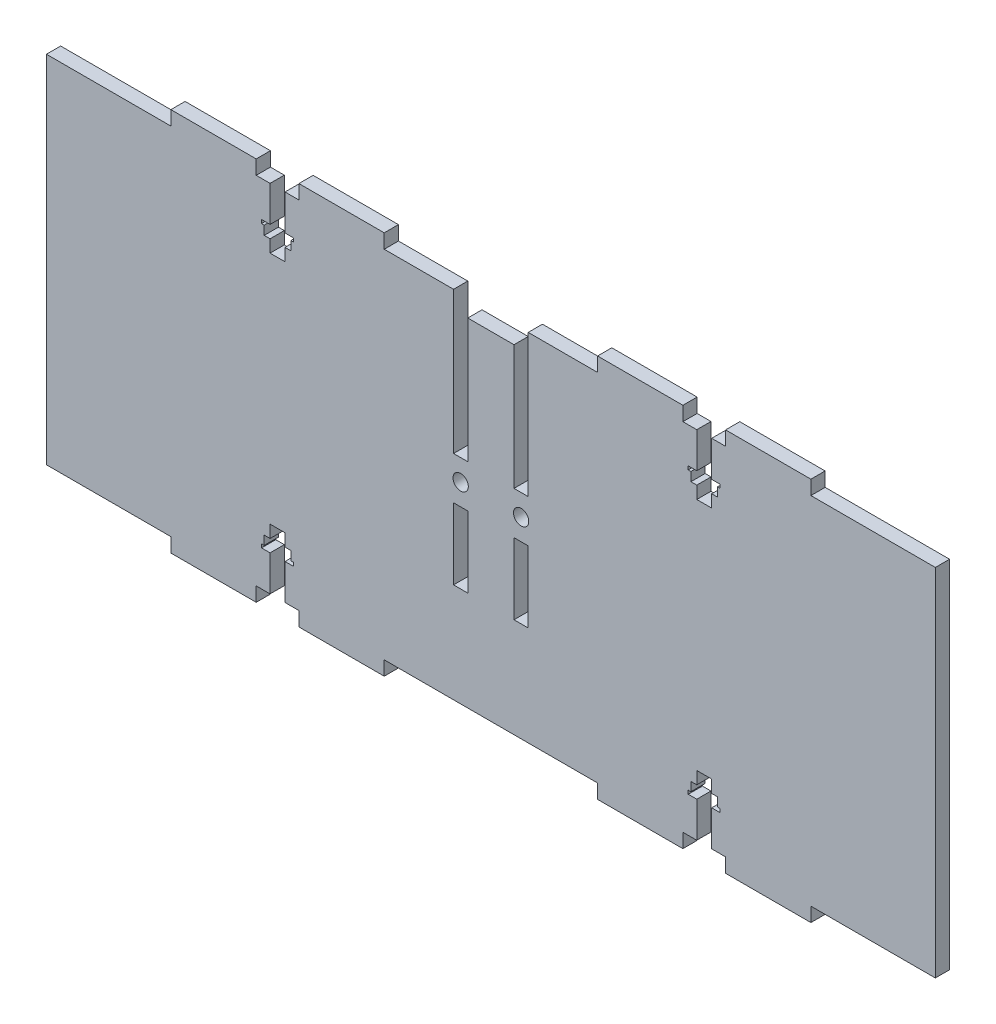
SolidWorks part; units mm, degrees
ref_plane "Front Plane" through (0, 0, 0) normal (0, 0, 1) x (1, 0, 0)
ref_plane "Top Plane" through (0, 0, 0) normal (0, 1, 0) x (1, 0, 0)
ref_plane "Right Plane" through (0, 0, 0) normal (1, 0, 0) x (0, 0, -1)
sketch "Sketch1" plane through (0, 0, 0) normal (0, 0, 1) x (1, 0, 0)
  line L1 (-125, 50) -> (125, 50)
  line L2 (-125, 50) -> (-125, -50)
  line L3 (-125, -50) -> (125, -50)
  line L4 (125, 50) -> (125, -50)
  line L5 (-125, 50) -> (125, -50) construction
  line L6 (-125, -50) -> (125, 50) construction
  point P0 (0, 0)
  dimension "D1" = 250
  dimension "D2" = 100
extrude "Boss-Extrude1" add sketch "Sketch1" along normal blind 4
sketch "Sketch2" plane through (0, -50, 0) normal (0, -1, 0) x (1, 0, 0)
  line L0 (-125, 4) -> (125, 4) construction
  line L1 (-66, 4) -> (-90, 4)
  line L2 (-66, 4) -> (-66, 0)
  line L3 (-66, 0) -> (-90, 0)
  line L4 (-90, 4) -> (-90, 0)
  line L5 (-125, 0) -> (125, 0) construction
  line L7 (-54, 4) -> (-30, 4)
  line L8 (-54, 4) -> (-54, 0)
  line L9 (-54, 0) -> (-30, 0)
  line L10 (-30, 4) -> (-30, 0)
  line L11 (-125, 4) -> (-125, 0) construction
  line L12 (0, 0) -> (0, 4) construction
  line L13 (30, 4) -> (30, 0)
  line L14 (54, 0) -> (30, 0)
  line L15 (54, 4) -> (54, 0)
  line L16 (54, 4) -> (30, 4)
  line L17 (90, 4) -> (90, 0)
  line L18 (66, 0) -> (90, 0)
  line L19 (66, 4) -> (66, 0)
  line L20 (66, 4) -> (90, 4)
  dimension "D1" = 24
  dimension "D2" = 35
  dimension "D3" = 12
  dimension "D4" = 24
extrude "Boss-Extrude2" add sketch "Sketch2" along normal blind 4
sketch "Sketch3" plane through (0, 0, 4) normal (0, 0, 1) x (1, 0, 0)
  line L0 (-8.5, 50) -> (-8.5, -50) construction
  line L1 (125, 50) -> (-125, 50) construction
  line L2 (-30, -50) -> (30, -50) construction
  line L3 (0, 50) -> (0, -50) construction
  line L4 (-10.5, 50) -> (-6.5, 50)
  line L5 (-10.5, 50) -> (-10.5, 10)
  line L6 (-10.5, 10) -> (-6.5, 10)
  line L7 (-6.5, 50) -> (-6.5, 10)
  line L8 (-10.5, 50) -> (-6.5, 10) construction
  line L9 (-10.5, 10) -> (-6.5, 50) construction
  line L10 (-10.5, -2) -> (-6.5, -2)
  line L11 (-10.5, -2) -> (-10.5, -22)
  line L12 (-10.5, -22) -> (-6.5, -22)
  line L13 (-6.5, -2) -> (-6.5, -22)
  line L14 (-10.5, -2) -> (-6.5, -22) construction
  line L15 (-10.5, -22) -> (-6.5, -2) construction
  line L16 (10.5, -22) -> (6.5, -2) construction
  line L17 (10.5, -2) -> (6.5, -22) construction
  line L18 (10.5, 10) -> (6.5, 50) construction
  line L19 (10.5, 50) -> (6.5, 10) construction
  line L20 (6.5, -2) -> (6.5, -22)
  line L21 (10.5, -22) -> (6.5, -22)
  line L22 (10.5, -2) -> (10.5, -22)
  line L23 (10.5, -2) -> (6.5, -2)
  line L24 (6.5, 50) -> (6.5, 10)
  line L25 (10.5, 10) -> (6.5, 10)
  line L26 (10.5, 50) -> (10.5, 10)
  line L27 (10.5, 50) -> (6.5, 50)
  point P6 (-8.5, 30)
  point P11 (-8.5, -12)
  point P26 (8.5, -12)
  point P27 (8.5, 30)
  dimension "D1" = 4
  dimension "D2" = 28
  dimension "D3" = 12
  dimension "D4" = 6.5
  dimension "D5" = 20
extrude "Cut-Extrude1" cut sketch "Sketch3" against normal through all
mirror "Mirror1" about plane through (0, 0, 0) normal (0, 1, 0) of "Boss-Extrude2"
hole_wizard "M4 Clearance Hole1" positions "Sketch5" profile "Sketch4" hole size "M4" standard "DIN"
sketch "Sketch5" plane through (0, 0, 4) normal (0, 0, 1) x (1, 0, 0)
  line L0 (-8.5, 10) -> (-8.5, -2) construction
  line L1 (-10.5, 10) -> (-6.5, 10) construction
  line L2 (-6.5, -2) -> (-10.5, -2) construction
  line L4 (8.5, 10) -> (8.5, -2) construction
  line L5 (6.5, 10) -> (10.5, 10) construction
  line L6 (10.5, -2) -> (6.5, -2) construction
  point P0 (-8.5, 4)
  point P19 (8.5, 4)
sketch "Sketch4" plane through (-8.5, 4, 4) normal (1, 0, 0) x (0, -1, 0)
  line L0 (0, 0) -> (0, 7.2919)
  line L1 (0, 7.2919) -> (2.15, 6)
  line L2 (2.15, 6) -> (2.15, 0)
  line L5 (2.15, 0) -> (0, 0)
  line L10 (0, 7.2919) -> (-2.15, 6) construction
  line L11 (0, -6.35) -> (0, 107.95) construction
  dimension "Hole Dia." = 4.3
  dimension "Hole Depth" = 6
  dimension "Drill Angle" = 118
sketch "Sketch6" plane through (0, 0, 4) normal (0, 0, 1) x (1, 0, 0)
  line L0 (-66, -50) -> (-54, -50) construction
  line L1 (60, -50) -> (60, -33) construction
  line L2 (57.9, -50) -> (57.9, -40)
  line L3 (62.1, -50) -> (62.1, -40)
  line L4 (56.25, -36.5) -> (57.9, -36.5)
  line L5 (56.25, -36.5) -> (56.25, -39)
  line L6 (62.1, -36.5) -> (62.1, -33)
  line L7 (63.75, -36.5) -> (63.75, -39)
  line L8 (55.5, -39) -> (55.5, -40)
  line L9 (64.5, -40) -> (62.1, -40)
  line L10 (62.1, -40) -> (64.5, -40)
  line L12 (0, 0) -> (0, -50) construction
  line L13 (-30, -50) -> (30, -50) construction
  line L14 (0, 0) -> (-125, 0) construction
  line L15 (-125, 50) -> (-125, -50) construction
  line L16 (64.5, -39) -> (64.5, -40)
  line L17 (64.5, -39) -> (63.75, -39)
  line L18 (62.1, -36.5) -> (62.1, -33)
  line L19 (63.75, -39) -> (64.5, -39)
  line L20 (57.9, -36.5) -> (56.25, -36.5)
  line L21 (56.25, -39) -> (55.5, -39)
  line L22 (62.1, -36.5) -> (63.75, -36.5)
  line L23 (57.9, -36.5) -> (57.9, -33)
  line L24 (57.9, -40) -> (55.5, -40)
  line L25 (56.25, -36.5) -> (56.25, -39)
  line L26 (57.9, -36.5) -> (57.9, -33)
  line L27 (55.5, -39) -> (56.25, -39)
  line L28 (55.5, -39) -> (55.5, -40)
  line L29 (55.5, -40) -> (57.9, -40)
  line L30 (64.5, -39) -> (64.5, -40)
  line L31 (63.75, -36.5) -> (63.75, -39)
  line L32 (63.75, -36.5) -> (62.1, -36.5)
  line L33 (57.9, -50) -> (57.9, -40)
  line L34 (62.1, -50) -> (62.1, -40)
  line L35 (57.9, -50) -> (57.9, -40)
  line L36 (62.1, -50) -> (62.1, -40)
  line L37 (56.25, -36.5) -> (57.9, -36.5)
  line L38 (56.25, -36.5) -> (56.25, -39)
  line L39 (55.5, -39) -> (55.5, -40)
  line L40 (64.5, -40) -> (62.1, -40)
  line L41 (64.5, -39) -> (64.5, -40)
  line L42 (64.5, -39) -> (63.75, -39)
  line L43 (62.1, -36.5) -> (62.1, -33)
  line L44 (63.75, -36.5) -> (63.75, -39)
  line L45 (62.1, -40) -> (64.5, -40)
  line L46 (62.1, -36.5) -> (62.1, -33)
  line L47 (57.9, -36.5) -> (56.25, -36.5)
  line L48 (63.75, -39) -> (64.5, -39)
  line L49 (-62.1, -50) -> (-57.9, -50)
  line L50 (-62.1, -50) -> (-62.1, -40)
  line L51 (-62.1, -33) -> (-57.9, -33)
  line L52 (-57.9, -50) -> (-57.9, -40)
  line L53 (-60, -50) -> (-60, -33) construction
  line L54 (-63.75, -36.5) -> (-62.1, -36.5)
  line L55 (-63.75, -36.5) -> (-63.75, -39)
  line L56 (-57.9, -36.5) -> (-57.9, -33)
  line L57 (-56.25, -36.5) -> (-56.25, -39)
  line L58 (-64.5, -39) -> (-64.5, -40)
  line L59 (-55.5, -40) -> (-57.9, -40)
  line L60 (-57.9, -40) -> (-55.5, -40)
  line L61 (-55.5, -39) -> (-55.5, -40)
  line L62 (-55.5, -39) -> (-56.25, -39)
  line L63 (-57.9, -36.5) -> (-57.9, -33)
  line L64 (-56.25, -39) -> (-55.5, -39)
  line L65 (-62.1, -36.5) -> (-63.75, -36.5)
  line L66 (-63.75, -39) -> (-64.5, -39)
  line L67 (-57.9, -36.5) -> (-56.25, -36.5)
  line L68 (-62.1, -36.5) -> (-62.1, -33)
  line L69 (-62.1, -40) -> (-64.5, -40)
  line L70 (-63.75, -36.5) -> (-63.75, -39)
  line L71 (-62.1, -36.5) -> (-62.1, -33)
  line L72 (-64.5, -39) -> (-63.75, -39)
  line L73 (-64.5, -39) -> (-64.5, -40)
  line L74 (-64.5, -40) -> (-62.1, -40)
  line L75 (-55.5, -39) -> (-55.5, -40)
  line L76 (-56.25, -36.5) -> (-56.25, -39)
  line L77 (-56.25, -36.5) -> (-57.9, -36.5)
  line L78 (-62.1, -50) -> (-62.1, -40)
  line L79 (-57.9, -50) -> (-57.9, -40)
  line L80 (-62.1, -50) -> (-62.1, -40)
  line L81 (-57.9, -50) -> (-57.9, -40)
  line L82 (-63.75, -36.5) -> (-62.1, -36.5)
  line L83 (-63.75, -36.5) -> (-63.75, -39)
  line L84 (-64.5, -39) -> (-64.5, -40)
  line L85 (-55.5, -40) -> (-57.9, -40)
  line L86 (-55.5, -39) -> (-55.5, -40)
  line L87 (-55.5, -39) -> (-56.25, -39)
  line L88 (-57.9, -36.5) -> (-57.9, -33)
  line L89 (-56.25, -36.5) -> (-56.25, -39)
  line L90 (-57.9, -40) -> (-55.5, -40)
  line L91 (-57.9, -36.5) -> (-57.9, -33)
  line L92 (-62.1, -36.5) -> (-63.75, -36.5)
  line L93 (-56.25, -39) -> (-55.5, -39)
  line L94 (-57.9, -36.5) -> (-56.25, -36.5)
  line L95 (-63.75, -39) -> (-64.5, -39)
  line L96 (-62.1, -36.5) -> (-62.1, -33)
  line L97 (-64.5, -39) -> (-63.75, -39)
  line L98 (-64.5, -39) -> (-64.5, -40)
  line L99 (-62.1, -40) -> (-64.5, -40)
  line L100 (-64.5, -40) -> (-62.1, -40)
  line L101 (-55.5, -39) -> (-55.5, -40)
  line L102 (-63.75, -36.5) -> (-63.75, -39)
  line L103 (-62.1, -36.5) -> (-62.1, -33)
  line L104 (-56.25, -36.5) -> (-56.25, -39)
  line L105 (-56.25, -36.5) -> (-57.9, -36.5)
  line L106 (-62.1, -50) -> (-62.1, -40)
  line L107 (-57.9, -50) -> (-57.9, -40)
  line L108 (62.1, -36.5) -> (63.75, -36.5)
  line L109 (56.25, -39) -> (55.5, -39)
  line L110 (57.9, -36.5) -> (57.9, -33)
  line L111 (55.5, -39) -> (56.25, -39)
  line L112 (55.5, -39) -> (55.5, -40)
  line L113 (57.9, -40) -> (55.5, -40)
  line L114 (55.5, -40) -> (57.9, -40)
  line L115 (64.5, -39) -> (64.5, -40)
  line L116 (56.25, -36.5) -> (56.25, -39)
  line L117 (57.9, -36.5) -> (57.9, -33)
  line L118 (63.75, -36.5) -> (63.75, -39)
  line L119 (63.75, -36.5) -> (62.1, -36.5)
  line L120 (57.9, -50) -> (57.9, -40)
  line L121 (62.1, -33) -> (57.9, -33)
  line L122 (62.1, -50) -> (62.1, -40)
  line L123 (62.1, -50) -> (57.9, -50)
  line L124 (-62.1, -50) -> (-62.1, -40)
  line L125 (-57.9, -50) -> (-57.9, -40)
  line L126 (-63.75, -36.5) -> (-62.1, -36.5)
  line L127 (-63.75, -36.5) -> (-63.75, -39)
  line L128 (-57.9, -36.5) -> (-57.9, -33)
  line L129 (-56.25, -36.5) -> (-56.25, -39)
  line L130 (-64.5, -39) -> (-64.5, -40)
  line L131 (-55.5, -40) -> (-57.9, -40)
  line L132 (-57.9, -40) -> (-55.5, -40)
  line L133 (-55.5, -39) -> (-55.5, -40)
  line L134 (-55.5, -39) -> (-56.25, -39)
  line L135 (-57.9, -36.5) -> (-57.9, -33)
  line L136 (-56.25, -39) -> (-55.5, -39)
  line L137 (-62.1, -36.5) -> (-63.75, -36.5)
  line L138 (-63.75, -39) -> (-64.5, -39)
  line L139 (-57.9, -36.5) -> (-56.25, -36.5)
  line L140 (-62.1, -36.5) -> (-62.1, -33)
  line L141 (-62.1, -40) -> (-64.5, -40)
  line L142 (-63.75, -36.5) -> (-63.75, -39)
  line L143 (-62.1, -36.5) -> (-62.1, -33)
  line L144 (-64.5, -39) -> (-63.75, -39)
  line L145 (-64.5, -39) -> (-64.5, -40)
  line L146 (-64.5, -40) -> (-62.1, -40)
  line L147 (-55.5, -39) -> (-55.5, -40)
  line L148 (-56.25, -36.5) -> (-56.25, -39)
  line L149 (-56.25, -36.5) -> (-57.9, -36.5)
  line L150 (-62.1, -50) -> (-62.1, -40)
  line L151 (-57.9, -50) -> (-57.9, -40)
  line L152 (-62.1, -50) -> (-62.1, -40)
  line L153 (-57.9, -50) -> (-57.9, -40)
  line L154 (-63.75, -36.5) -> (-62.1, -36.5)
  line L155 (-63.75, -36.5) -> (-63.75, -39)
  line L156 (-64.5, -39) -> (-64.5, -40)
  line L157 (-55.5, -40) -> (-57.9, -40)
  line L158 (-55.5, -39) -> (-55.5, -40)
  line L159 (-55.5, -39) -> (-56.25, -39)
  line L160 (-57.9, -36.5) -> (-57.9, -33)
  line L161 (-56.25, -36.5) -> (-56.25, -39)
  line L162 (-57.9, -40) -> (-55.5, -40)
  line L163 (-57.9, -36.5) -> (-57.9, -33)
  line L164 (-62.1, -36.5) -> (-63.75, -36.5)
  line L165 (-56.25, -39) -> (-55.5, -39)
  line L166 (-57.9, -36.5) -> (-56.25, -36.5)
  line L167 (-63.75, -39) -> (-64.5, -39)
  line L168 (-62.1, -36.5) -> (-62.1, -33)
  line L169 (-64.5, -39) -> (-63.75, -39)
  line L170 (-64.5, -39) -> (-64.5, -40)
  line L171 (-62.1, -40) -> (-64.5, -40)
  line L172 (-64.5, -40) -> (-62.1, -40)
  line L173 (-55.5, -39) -> (-55.5, -40)
  line L174 (-63.75, -36.5) -> (-63.75, -39)
  line L175 (-62.1, -36.5) -> (-62.1, -33)
  line L176 (-56.25, -36.5) -> (-56.25, -39)
  line L177 (-56.25, -36.5) -> (-57.9, -36.5)
  line L178 (-62.1, -50) -> (-62.1, -40)
  line L179 (-57.9, -50) -> (-57.9, -40)
  line L180 (60, 50) -> (60, 33) construction
  line L181 (62.1, 50) -> (57.9, 50)
  line L182 (62.1, 50) -> (62.1, 40)
  line L183 (62.1, 33) -> (57.9, 33)
  line L184 (57.9, 50) -> (57.9, 40)
  line L185 (63.75, 36.5) -> (62.1, 36.5)
  line L186 (63.75, 36.5) -> (63.75, 39)
  line L187 (57.9, 36.5) -> (57.9, 33)
  line L188 (56.25, 36.5) -> (56.25, 39)
  line L189 (64.5, 39) -> (64.5, 40)
  line L190 (55.5, 40) -> (57.9, 40)
  line L191 (57.9, 40) -> (55.5, 40)
  line L192 (55.5, 39) -> (55.5, 40)
  line L193 (55.5, 39) -> (56.25, 39)
  line L194 (57.9, 36.5) -> (57.9, 33)
  line L195 (56.25, 39) -> (55.5, 39)
  line L196 (62.1, 36.5) -> (63.75, 36.5)
  line L197 (63.75, 39) -> (64.5, 39)
  line L198 (57.9, 36.5) -> (56.25, 36.5)
  line L199 (62.1, 36.5) -> (62.1, 33)
  line L200 (62.1, 40) -> (64.5, 40)
  line L201 (63.75, 36.5) -> (63.75, 39)
  line L202 (62.1, 36.5) -> (62.1, 33)
  line L203 (64.5, 39) -> (63.75, 39)
  line L204 (64.5, 39) -> (64.5, 40)
  line L205 (64.5, 40) -> (62.1, 40)
  line L206 (55.5, 39) -> (55.5, 40)
  line L207 (56.25, 36.5) -> (56.25, 39)
  line L208 (56.25, 36.5) -> (57.9, 36.5)
  line L209 (62.1, 50) -> (62.1, 40)
  line L210 (57.9, 50) -> (57.9, 40)
  line L211 (62.1, 50) -> (62.1, 40)
  line L212 (57.9, 50) -> (57.9, 40)
  line L213 (63.75, 36.5) -> (62.1, 36.5)
  line L214 (63.75, 36.5) -> (63.75, 39)
  line L215 (64.5, 39) -> (64.5, 40)
  line L216 (55.5, 40) -> (57.9, 40)
  line L217 (55.5, 39) -> (55.5, 40)
  line L218 (55.5, 39) -> (56.25, 39)
  line L219 (57.9, 36.5) -> (57.9, 33)
  line L220 (56.25, 36.5) -> (56.25, 39)
  line L221 (57.9, 40) -> (55.5, 40)
  line L222 (57.9, 36.5) -> (57.9, 33)
  line L223 (62.1, 36.5) -> (63.75, 36.5)
  line L224 (56.25, 39) -> (55.5, 39)
  line L225 (57.9, 36.5) -> (56.25, 36.5)
  line L226 (63.75, 39) -> (64.5, 39)
  line L227 (62.1, 36.5) -> (62.1, 33)
  line L228 (64.5, 39) -> (63.75, 39)
  line L229 (64.5, 39) -> (64.5, 40)
  line L230 (62.1, 40) -> (64.5, 40)
  line L231 (64.5, 40) -> (62.1, 40)
  line L232 (55.5, 39) -> (55.5, 40)
  line L233 (63.75, 36.5) -> (63.75, 39)
  line L234 (62.1, 36.5) -> (62.1, 33)
  line L235 (56.25, 36.5) -> (56.25, 39)
  line L236 (56.25, 36.5) -> (57.9, 36.5)
  line L237 (62.1, 50) -> (62.1, 40)
  line L238 (57.9, 50) -> (57.9, 40)
  line L239 (-60, 50) -> (-60, 33) construction
  line L240 (-57.9, 50) -> (-57.9, 40)
  line L241 (-62.1, 50) -> (-62.1, 40)
  line L242 (-56.25, 36.5) -> (-57.9, 36.5)
  line L243 (-56.25, 36.5) -> (-56.25, 39)
  line L244 (-62.1, 36.5) -> (-62.1, 33)
  line L245 (-63.75, 36.5) -> (-63.75, 39)
  line L246 (-55.5, 39) -> (-55.5, 40)
  line L247 (-64.5, 40) -> (-62.1, 40)
  line L248 (-62.1, 40) -> (-64.5, 40)
  line L249 (-64.5, 39) -> (-64.5, 40)
  line L250 (-64.5, 39) -> (-63.75, 39)
  line L251 (-62.1, 36.5) -> (-62.1, 33)
  line L252 (-63.75, 39) -> (-64.5, 39)
  line L253 (-57.9, 36.5) -> (-56.25, 36.5)
  line L254 (-56.25, 39) -> (-55.5, 39)
  line L255 (-62.1, 36.5) -> (-63.75, 36.5)
  line L256 (-57.9, 36.5) -> (-57.9, 33)
  line L257 (-57.9, 40) -> (-55.5, 40)
  line L258 (-56.25, 36.5) -> (-56.25, 39)
  line L259 (-57.9, 36.5) -> (-57.9, 33)
  line L260 (-55.5, 39) -> (-56.25, 39)
  line L261 (-55.5, 39) -> (-55.5, 40)
  line L262 (-55.5, 40) -> (-57.9, 40)
  line L263 (-64.5, 39) -> (-64.5, 40)
  line L264 (-63.75, 36.5) -> (-63.75, 39)
  line L265 (-63.75, 36.5) -> (-62.1, 36.5)
  line L266 (-57.9, 50) -> (-57.9, 40)
  line L267 (-62.1, 50) -> (-62.1, 40)
  line L268 (-57.9, 50) -> (-57.9, 40)
  line L269 (-62.1, 50) -> (-62.1, 40)
  line L270 (-56.25, 36.5) -> (-57.9, 36.5)
  line L271 (-56.25, 36.5) -> (-56.25, 39)
  line L272 (-55.5, 39) -> (-55.5, 40)
  line L273 (-64.5, 40) -> (-62.1, 40)
  line L274 (-64.5, 39) -> (-64.5, 40)
  line L275 (-64.5, 39) -> (-63.75, 39)
  line L276 (-62.1, 36.5) -> (-62.1, 33)
  line L277 (-63.75, 36.5) -> (-63.75, 39)
  line L278 (-62.1, 40) -> (-64.5, 40)
  line L279 (-62.1, 36.5) -> (-62.1, 33)
  line L280 (-57.9, 36.5) -> (-56.25, 36.5)
  line L281 (-63.75, 39) -> (-64.5, 39)
  line L282 (-62.1, 36.5) -> (-63.75, 36.5)
  line L283 (-56.25, 39) -> (-55.5, 39)
  line L284 (-57.9, 36.5) -> (-57.9, 33)
  line L285 (-55.5, 39) -> (-56.25, 39)
  line L286 (-55.5, 39) -> (-55.5, 40)
  line L287 (-57.9, 40) -> (-55.5, 40)
  line L288 (-55.5, 40) -> (-57.9, 40)
  line L289 (-64.5, 39) -> (-64.5, 40)
  line L290 (-56.25, 36.5) -> (-56.25, 39)
  line L291 (-57.9, 36.5) -> (-57.9, 33)
  line L292 (-63.75, 36.5) -> (-63.75, 39)
  line L293 (-63.75, 36.5) -> (-62.1, 36.5)
  line L294 (-57.9, 50) -> (-57.9, 40)
  line L295 (-62.1, 50) -> (-62.1, 40)
  line L296 (-57.9, 50) -> (-57.9, 40)
  line L297 (-62.1, 50) -> (-62.1, 40)
  line L298 (-56.25, 36.5) -> (-57.9, 36.5)
  line L299 (-56.25, 36.5) -> (-56.25, 39)
  line L300 (-62.1, 36.5) -> (-62.1, 33)
  line L301 (-63.75, 36.5) -> (-63.75, 39)
  line L302 (-55.5, 39) -> (-55.5, 40)
  line L303 (-64.5, 40) -> (-62.1, 40)
  line L304 (-62.1, 40) -> (-64.5, 40)
  line L305 (-64.5, 39) -> (-64.5, 40)
  line L306 (-64.5, 39) -> (-63.75, 39)
  line L307 (-62.1, 36.5) -> (-62.1, 33)
  line L308 (-63.75, 39) -> (-64.5, 39)
  line L309 (-57.9, 36.5) -> (-56.25, 36.5)
  line L310 (-56.25, 39) -> (-55.5, 39)
  line L311 (-62.1, 36.5) -> (-63.75, 36.5)
  line L312 (-57.9, 36.5) -> (-57.9, 33)
  line L313 (-57.9, 40) -> (-55.5, 40)
  line L314 (-56.25, 36.5) -> (-56.25, 39)
  line L315 (-57.9, 36.5) -> (-57.9, 33)
  line L316 (-55.5, 39) -> (-56.25, 39)
  line L317 (-55.5, 39) -> (-55.5, 40)
  line L318 (-55.5, 40) -> (-57.9, 40)
  line L319 (-64.5, 39) -> (-64.5, 40)
  line L320 (-63.75, 36.5) -> (-63.75, 39)
  line L321 (-63.75, 36.5) -> (-62.1, 36.5)
  line L322 (-57.9, 50) -> (-57.9, 40)
  line L323 (-62.1, 50) -> (-62.1, 40)
  line L324 (-57.9, 50) -> (-57.9, 40)
  line L325 (-62.1, 50) -> (-62.1, 40)
  line L326 (-56.25, 36.5) -> (-57.9, 36.5)
  line L327 (-56.25, 36.5) -> (-56.25, 39)
  line L328 (-55.5, 39) -> (-55.5, 40)
  line L329 (-64.5, 40) -> (-62.1, 40)
  line L330 (-64.5, 39) -> (-64.5, 40)
  line L331 (-64.5, 39) -> (-63.75, 39)
  line L332 (-62.1, 36.5) -> (-62.1, 33)
  line L333 (-63.75, 36.5) -> (-63.75, 39)
  line L334 (-62.1, 40) -> (-64.5, 40)
  line L335 (-62.1, 36.5) -> (-62.1, 33)
  line L336 (-57.9, 36.5) -> (-56.25, 36.5)
  line L337 (-63.75, 39) -> (-64.5, 39)
  line L338 (-62.1, 36.5) -> (-63.75, 36.5)
  line L339 (-56.25, 39) -> (-55.5, 39)
  line L340 (-57.9, 36.5) -> (-57.9, 33)
  line L341 (-55.5, 39) -> (-56.25, 39)
  line L342 (-55.5, 39) -> (-55.5, 40)
  line L343 (-57.9, 40) -> (-55.5, 40)
  line L344 (-55.5, 40) -> (-57.9, 40)
  line L345 (-64.5, 39) -> (-64.5, 40)
  line L346 (-56.25, 36.5) -> (-56.25, 39)
  line L347 (-57.9, 36.5) -> (-57.9, 33)
  line L348 (-63.75, 36.5) -> (-63.75, 39)
  line L349 (-63.75, 36.5) -> (-62.1, 36.5)
  line L350 (-57.9, 50) -> (-57.9, 40)
  line L351 (-62.1, 33) -> (-57.9, 33)
  line L352 (-62.1, 50) -> (-62.1, 40)
  line L353 (-62.1, 50) -> (-57.9, 50)
  dimension "D2" = 10
  dimension "D6" = 4.2
  dimension "D7" = 17
  dimension "D8" = 7.5
  dimension "D9" = 2.5
  dimension "D10" = 9
  dimension "D11" = 1
extrude "Cut-Extrude2" cut sketch "Sketch6" against normal blind 10
sketch "Sketch7" plane through (0, 0, 4) normal (0, 0, 1) x (1, 0, 0)
  line L0 (6.5, 50) -> (6.5, 10) construction
  line L1 (-6.5, 50) -> (6.5, 50)
  line L2 (-6.5, 50) -> (-6.5, 45)
  line L3 (-6.5, 45) -> (6.5, 45)
  line L4 (6.5, 50) -> (6.5, 45)
  dimension "D1" = 5
extrude "Cut-Extrude3" cut sketch "Sketch7" against normal blind 10
